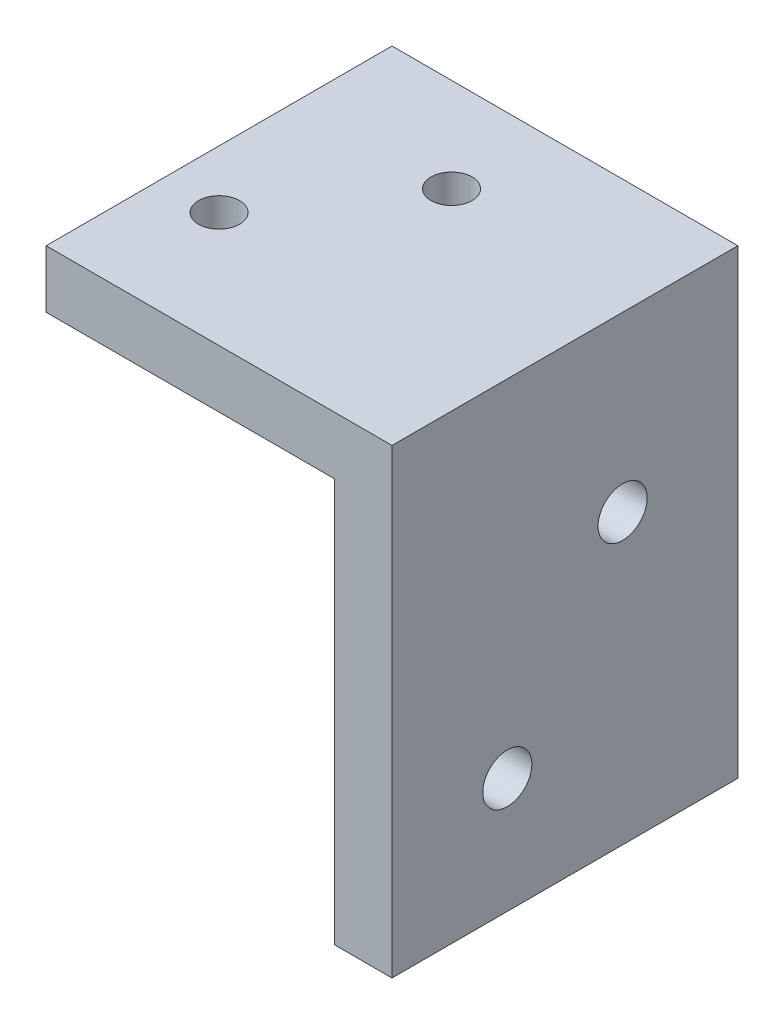
SolidWorks part; units mm, degrees
ref_plane "Front Plane" through (0, 0, 0) normal (0, 0, 1) x (1, 0, 0)
ref_plane "Top Plane" through (0, 0, 0) normal (0, 1, 0) x (1, 0, 0)
ref_plane "Right Plane" through (0, 0, 0) normal (1, 0, 0) x (0, 0, -1)
sketch "Sketch1" plane through (0, 0, 0) normal (0, 0, 1) x (1, 0, 0)
  line L1 (-59.9071, 30.8316) -> (-40.8571, 30.8316)
  line L2 (-59.9071, 30.8316) -> (-59.9071, 27.6566)
  line L3 (-44.0321, 5.4316) -> (-40.8571, 5.4316)
  line L4 (-40.8571, 30.8316) -> (-40.8571, 5.4316)
  line L5 (-59.9071, 27.6566) -> (-44.0321, 27.6566)
  line L8 (-44.0321, 27.6566) -> (-44.0321, 5.4316)
  dimension "D1" = 3.175
  dimension "D2" = 3.175
  dimension "D3" = 25.4
  dimension "D4" = 19.05
extrude "Boss-Extrude1" add sketch "Sketch1" along normal blind 6.35 and the other way blind 12.7
hole_wizard "Tap Drill for #6-32 Tap1" positions "3DSketch1" profile "Sketch4" hole size "#6-32" standard "ANSI Inch" end condition through all
sketch3d "3DSketch1"
  line L0 (-44.0321, 27.6566, 6.35) -> (-44.0321, 5.4316, 6.35) construction
  line L1 (-44.0321, 27.6566, -12.7) -> (-44.0321, 5.4316, -12.7) construction
  line L2 (-44.0321, 5.4316, -12.7) -> (-44.0321, 5.4316, 6.35) construction
  line L3 (-44.0321, 27.6566, -12.7) -> (-44.0321, 27.6566, 6.35) construction
  point P0 (-44.0321, 11.7816, 0)
  point P2 (-44.0321, 21.3066, -6.35)
  dimension "D1" = 6.35
  dimension "D2" = 6.35
  dimension "D3" = 6.35
  dimension "D4" = 6.35
sketch "Sketch4" plane through (-44.0321, 11.7816, 0) normal (0, 1, 0) x (0, 0, 1)
  line L0 (0, 0) -> (0, 3.175)
  line L1 (0, 3.175) -> (1.3525, 3.175)
  line L2 (1.3525, 3.175) -> (1.3525, 0)
  line L5 (1.3525, 0) -> (0, 0)
  line L11 (0, -6.35) -> (0, 107.95) construction
  dimension "Thru Hole Dia." = 2.7051
  dimension "Thru Hole Depth" = 3.175
sketch "Sketch5" plane through (0, 30.8316, 0) normal (0, 1, 0) x (1, 0, 0)
  line L0 (-59.9071, 12.7) -> (-59.9071, -6.35) construction
  line L2 (-51.4582, 7.5319) -> (-56.7321, 0)
  line L3 (-40.8571, 12.7) -> (-40.8571, -6.35) construction
  line L4 (-40.8571, -6.35) -> (-59.9071, -6.35) construction
  circle A0 centre (-51.4582, 7.5319) radius 0.6599
  circle A1 centre (-56.7321, 0) radius 0.8384
  dimension "D1" = 9.1948
  dimension "D2" = 35
  dimension "D3" = 3.175
  dimension "D4" = 6.35
hole_wizard "Tap Drill for #4-40 Tap1" positions "3DSketch2" profile "Sketch6" hole size "#4-40" standard "ANSI Inch"
sketch3d "3DSketch2"
  point P0 (-51.4582, 30.8316, -7.5319)
  point P3 (-56.7321, 30.8316, 0)
sketch "Sketch6" plane through (-51.4582, 30.8316, -7.5319) normal (1, 0, 0) x (0, 0, 1)
  line L0 (0, 0) -> (0, 3.9812)
  line L1 (0, 3.9812) -> (1.1303, 3.302)
  line L2 (1.1303, 3.302) -> (1.1303, 0)
  line L5 (1.1303, 0) -> (0, 0)
  line L10 (0, 3.9812) -> (-1.1303, 3.302) construction
  line L11 (0, -6.35) -> (0, 107.95) construction
  dimension "Hole Dia." = 2.2606
  dimension "Hole Depth" = 3.302
  dimension "Drill Angle" = 118
